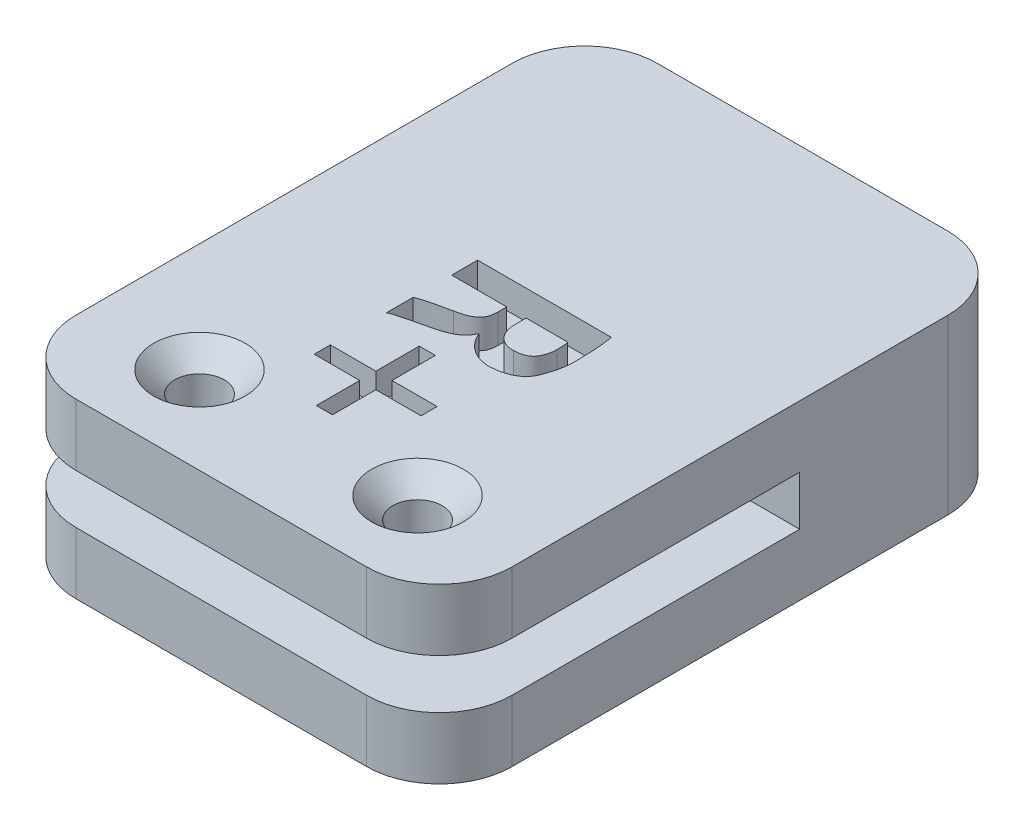
SolidWorks part; units mm, degrees
ref_plane "Front Plane" through (0, 0, 0) normal (0, 0, 1) x (1, 0, 0)
ref_plane "Top Plane" through (0, 0, 0) normal (0, 1, 0) x (1, 0, 0)
ref_plane "Right Plane" through (0, 0, 0) normal (1, 0, 0) x (0, 0, -1)
sketch "Sketch1" plane through (0, 0, 0) normal (0, 1, 0) x (1, 0, 0)
  line L0 (15, 15) -> (15, 20)
  line L1 (-10, -20) -> (10, -20)
  line L2 (-15, -15) -> (-15, 15)
  line L3 (-10, 20) -> (10, 20)
  line L4 (15, -15) -> (15, 15)
  line L5 (-15, -20) -> (15, 20) construction
  line L6 (-15, 20) -> (15, -20) construction
  line L7 (15, 20) -> (10, 20)
  arc A0 (15, -15) -> (10, -20) centre (10, -15) cw
  arc A1 (-10, -20) -> (-15, -15) centre (-10, -15) cw
  arc A2 (15, 15) -> (10, 20) centre (10, 15) ccw construction
  arc A3 (-10, 20) -> (-15, 15) centre (-10, 15) ccw
  point P0 (0, 0)
  dimension "D3" = 5
  dimension "D1" = 30
  dimension "D2" = 40
extrude "Boss-Extrude1" add sketch "Sketch1" along normal blind 4.25
sketch "Sketch2" plane through (0, 4.25, 0) normal (0, 1, 0) x (1, 0, 0)
  line L1 (-7.5, -14) -> (7.5, -14) construction
  line L2 (-7.5, -14) -> (-7.5, 14) construction
  line L3 (-7.5, 14) -> (7.5, 14) construction
  line L4 (7.5, -14) -> (7.5, 14) construction
  line L5 (-7.5, -14) -> (7.5, 14) construction
  line L6 (-7.5, 14) -> (7.5, -14) construction
  point P0 (0, 0)
  dimension "D1" = 28
  dimension "D2" = 15
sketch "Sketch7" plane through (0, 4.25, 0) normal (0, 1, 0) x (1, 0, 0)
  line L2 (4.5, 0) -> (4.5, 20) construction
  line L4 (0, 0) -> (4.5, 0) construction
  text T0 "R- " font "@Adobe Gothic Std B" height in points 30
  dimension "D1" = 4.5
extrude "Cut-Extrude1" [suppressed] cut sketch "Sketch7" against normal blind 2
sketch "Sketch8" plane through (15, 0, 0) normal (1, 0, 0) x (0, 0, -1)
  line L0 (-15, 0) -> (20, 0) construction
  line L1 (4.788, 0) -> (20, 0)
  line L2 (4.788, 0) -> (4.788, -3.4)
  line L3 (5.2539, -7.65) -> (20, -7.65)
  line L4 (20, 0) -> (20, -7.65)
  line L5 (20, 4.25) -> (20, 0) construction
  line L6 (4.788, -3) -> (4.788, 0) construction
  line L7 (-35.212, -3) -> (4.788, -3) construction
  line L8 (5.2539, -7.65) -> (-20, -7.65)
  line L10 (4.788, -3.4) -> (-20, -3.4)
  line L11 (-20, -7.65) -> (-20, -3.4)
  line L12 (-20, 4.25) -> (-20, 0) construction
  dimension "D1" = 0
  dimension "D2" = 0.4
  dimension "D3" = 4.25
extrude "Boss-Extrude2" add sketch "Sketch8" against normal up to surface (30 mm away) up to face at (-15, 2.125, 0)
fillet "Fillet1" radius 5 4 edges at (-15, -5.525, 20) (15, -5.525, 20) (-15, -3.825, -20) (15, -1.7, -20)
hole_wizard "CSK for M3 Countersunk Flat Head Screw1" positions "3DSketch1" profile "Sketch3" countersink size "M3" standard "DIN"
sketch3d "3DSketch1"
  point P6 (7.5, 4.25, 14)
  point P9 (-7.5, 4.25, 14)
  point P12 (7.5, 4.25, -14)
  point P14 (7.5, 4.25, -14)
  point P16 (7.5, 4.25, -14)
sketch "Sketch3" plane through (7.5, 4.25, 14) normal (1, 0, 0) x (0, 0, 1)
  line L0 (0, 0) -> (0, 11.9)
  line L1 (0, 11.9) -> (1.7, 11.9)
  line L2 (1.7, 11.9) -> (1.7, 1.45)
  line L3 (1.7, 1.45) -> (3.15, 0)
  line L5 (3.15, 0) -> (0, 0)
  line L6 (-1.7, 1.45) -> (-3.15, 0) construction
  line L11 (0, -6.35) -> (0, 107.95) construction
  dimension "Thru Hole Dia." = 3.4
  dimension "Thru Hole Depth" = 11.9
  dimension "Near C'Sink Dia." = 6.3
  dimension "Near C'Sink Angle" = 90
sketch "Sketch9" plane through (0, 0, 0) normal (0, -1, 0) x (1, 0, 0)
  arc A0 (-103.3954, -42.734) -> (-100.7142, -44.9838) centre (-102.0548, -43.8589) ccw construction
  arc A1 (-100.7142, -44.9838) -> (-103.3954, -42.734) centre (-102.0548, -43.8589) ccw construction
  arc A2 (-107.8949, -48.0963) -> (-105.2137, -50.3461) centre (-106.5543, -49.2212) ccw construction
  arc A3 (-105.2137, -50.3461) -> (-107.8949, -48.0963) centre (-106.5543, -49.2212) ccw construction
  arc A4 (-103.3954, -42.734) -> (-100.7142, -44.9838) centre (-102.0548, -43.8589) ccw construction
  arc A5 (-100.7142, -44.9838) -> (-103.3954, -42.734) centre (-102.0548, -43.8589) ccw construction
  arc A6 (-107.8949, -48.0963) -> (-105.2137, -50.3461) centre (-106.5543, -49.2212) ccw construction
  arc A7 (-105.2137, -50.3461) -> (-107.8949, -48.0963) centre (-106.5543, -49.2212) ccw construction
  point P5 (-102.0548, -43.8589)
  point P10 (-106.5543, -49.2212)
hole_wizard "CSK for M3 Countersunk Flat Head Screw2" [suppressed] positions "3DSketch4" profile "Sketch14" countersink size "M3" standard "DIN"
sketch3d "3DSketch4"
  point P0 (-102.0548, 0, -43.8589)
  point P3 (-106.5543, 0, -49.2212)
sketch "Sketch14" plane through (-102.0548, 0, -43.8589) normal (1, 0, 0) x (0, 0, -1)
  line L0 (0, 0) -> (0, 21.0215)
  line L1 (0, 21.0215) -> (1.7, 20)
  line L2 (1.7, 20) -> (1.7, 1.65)
  line L3 (1.7, 1.65) -> (3.35, 0)
  line L5 (3.35, 0) -> (0, 0)
  line L6 (-1.7, 1.65) -> (-3.35, 0) construction
  line L10 (0, 21.0215) -> (-1.7, 20) construction
  line L11 (0, -6.35) -> (0, 107.95) construction
  dimension "Hole Dia." = 3.4
  dimension "Hole Depth" = 20
  dimension "Near C'Sink Dia." = 6.7
  dimension "Near C'Sink Angle" = 90
  dimension "Drill Angle" = 118
sketch "Sketch15" [suppressed] plane through (0, -7.65, 0) normal (0, -1, 0) x (1, 0, 0)
  line L0 (15, 15) -> (15, -15) construction
  line L1 (-8, 9.1065) -> (6, 9.1065)
  line L2 (-10, 7.1065) -> (-10, -0.8935)
  line L3 (-8, -2.8935) -> (6, -2.8935)
  line L4 (8, 7.1065) -> (8, -0.8935)
  line L5 (-10, 9.1065) -> (8, -2.8935) construction
  line L6 (-10, -2.8935) -> (8, 9.1065) construction
  line L7 (-15, -15) -> (-15, 15) construction
  arc A0 (-8, 9.1065) -> (-10, 7.1065) centre (-8, 7.1065) ccw
  arc A1 (-10, -0.8935) -> (-8, -2.8935) centre (-8, -0.8935) ccw
  arc A2 (6, -2.8935) -> (8, -0.8935) centre (6, -0.8935) ccw
  arc A3 (8, 7.1065) -> (6, 9.1065) centre (6, 7.1065) ccw
  point P0 (-1, 3.1065)
  dimension "D5" = 2
  dimension "D1" = 6
  dimension "D2" = 6
  dimension "D3" = 7
  dimension "D4" = 5
extrude "Cut-Extrude2" [suppressed] cut sketch "Sketch15" against normal up to surface (4.25 mm away)
sketch "Sketch16" plane through (0, 4.25, 0) normal (0, 1, 0) x (1, 0, 0)
  line L0 (0, 0) -> (-4.5, 0) construction
  line L3 (-4.5, 3) -> (-4.5, -7.8869) construction
  text T0 "R+" font "@Adobe Gothic Std B" height in points 30
  dimension "D1" = 4.5
  dimension "D2" = 3
extrude "Cut-Extrude3" cut sketch "Sketch16" against normal blind 2
sketch "Sketch17" plane through (0, 4.25, 0) normal (0, 1, 0) x (1, 0, 0)
  arc A0 (0.4164, 34.0701) -> (-1.6598, 31.2524) centre (-0.6217, 32.6613) ccw construction
  arc A1 (-1.6598, 31.2524) -> (0.4164, 34.0701) centre (-0.6217, 32.6613) ccw construction
  arc A2 (6.0517, 29.9177) -> (3.9755, 27.1) centre (5.0136, 28.5088) ccw construction
  arc A3 (3.9755, 27.1) -> (6.0517, 29.9177) centre (5.0136, 28.5088) ccw construction
  arc A4 (0.4164, 34.0701) -> (-1.6598, 31.2524) centre (-0.6217, 32.6613) ccw construction
  arc A5 (-1.6598, 31.2524) -> (0.4164, 34.0701) centre (-0.6217, 32.6613) ccw construction
  arc A6 (6.0517, 29.9177) -> (3.9755, 27.1) centre (5.0136, 28.5088) ccw construction
  arc A7 (3.9755, 27.1) -> (6.0517, 29.9177) centre (5.0136, 28.5088) ccw construction
  point P5 (5.0136, 28.5088)
sketch "Sketch19" plane through (0, -7.65, 0) normal (0, -1, 0) x (1, 0, 0)
  arc A0 (-1.6598, -31.2524) -> (0.4164, -34.0701) centre (-0.6217, -32.6613) ccw construction
  arc A1 (0.4164, -34.0701) -> (-1.6598, -31.2524) centre (-0.6217, -32.6613) ccw construction
  arc A2 (3.9755, -27.1) -> (6.0517, -29.9177) centre (5.0136, -28.5088) ccw construction
  arc A3 (6.0517, -29.9177) -> (3.9755, -27.1) centre (5.0136, -28.5088) ccw construction
  arc A4 (-1.6598, -31.2524) -> (0.4164, -34.0701) centre (-0.6217, -32.6613) ccw
  arc A5 (0.4164, -34.0701) -> (-1.6598, -31.2524) centre (-0.6217, -32.6613) ccw
  arc A6 (3.9755, -27.1) -> (6.0517, -29.9177) centre (5.0136, -28.5088) ccw
  arc A7 (6.0517, -29.9177) -> (3.9755, -27.1) centre (5.0136, -28.5088) ccw
  point P0 (-0.6217, -32.6613)
  point P2 (5.0136, -28.5088)
hole_wizard "CSK for M3 Countersunk Flat Head Screw3" positions "3DSketch5" profile "Sketch20" countersink size "M3" standard "DIN"
sketch3d "3DSketch5"
  point P0 (5.0136, -7.65, -28.5088)
  point P3 (-0.6217, -7.65, -32.6613)
sketch "Sketch20" plane through (5.0136, -7.65, -28.5088) normal (1, 0, 0) x (0, 0, -1)
  line L0 (0, 0) -> (0, 21.0215)
  line L1 (0, 21.0215) -> (1.7, 20)
  line L2 (1.7, 20) -> (1.7, 1.65)
  line L3 (1.7, 1.65) -> (3.35, 0)
  line L5 (3.35, 0) -> (0, 0)
  line L6 (-1.7, 1.65) -> (-3.35, 0) construction
  line L10 (0, 21.0215) -> (-1.7, 20) construction
  line L11 (0, -6.35) -> (0, 107.95) construction
  dimension "Hole Dia." = 3.4
  dimension "Hole Depth" = 20
  dimension "Near C'Sink Dia." = 6.7
  dimension "Near C'Sink Angle" = 90
  dimension "Drill Angle" = 118
